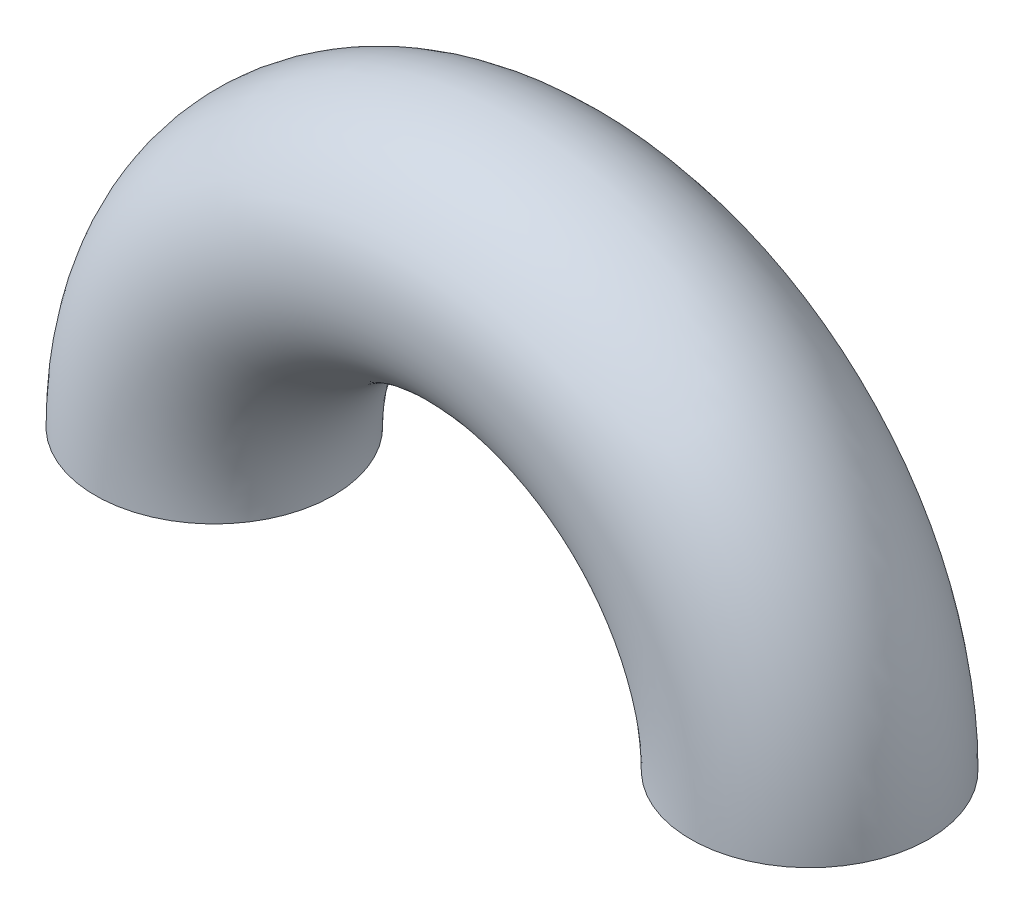
SolidWorks part; units mm, degrees
material "Beryllium Copper, UNS C17200"
ref_plane "Front Plane" through (0, 0, 0) normal (0, 0, 1) x (1, 0, 0)
ref_plane "Top Plane" through (0, 0, 0) normal (0, 1, 0) x (1, 0, 0)
ref_plane "Right Plane" through (0, 0, 0) normal (1, 0, 0) x (0, 0, -1)
sketch "Sketch1" plane through (0, 0, 0) normal (0, 0, 1) x (1, 0, 0)
  arc A0 (-12.5, 0) -> (12.5, 0) centre (0, 0) cw
  dimension "D1" = 12.5
sketch "Sketch2" plane through (0, 0, 0) normal (0, 1, 0) x (1, 0, 0)
  circle A0 centre (-12.5, 0) radius 5
  dimension "D1" = 10
sweep "Sweep1" add profiles "Sketch2" path "Sketch1"
shell "Shell1" thickness 0.5
